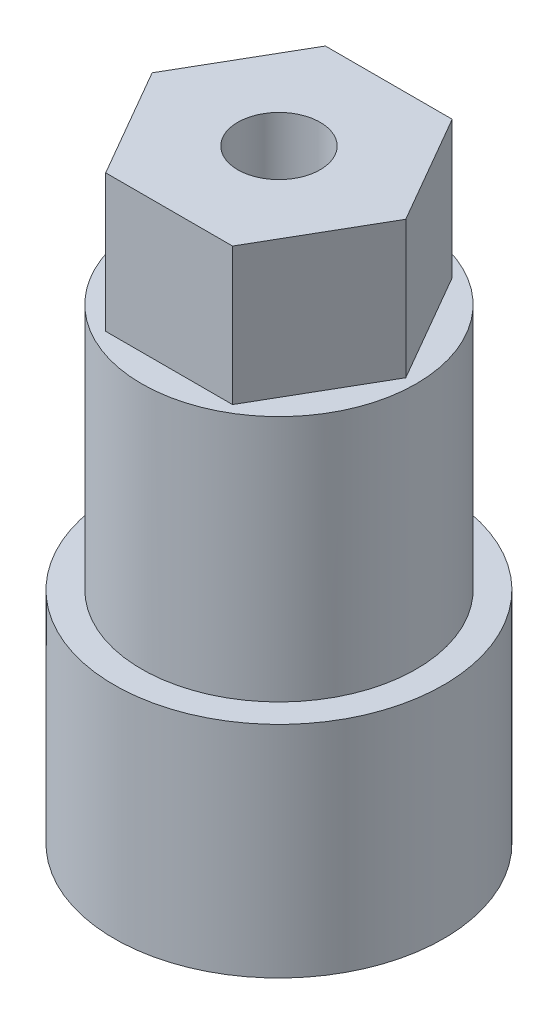
SolidWorks part; units mm, degrees
material "Nylon 101"
ref_plane "Front Plane" through (0, 0, 0) normal (0, 0, 1) x (1, 0, 0)
ref_plane "Top Plane" through (0, 0, 0) normal (0, 1, 0) x (1, 0, 0)
ref_plane "Right Plane" through (0, 0, 0) normal (1, 0, 0) x (0, 0, -1)
sketch "Sketch1" plane through (0, 0, 0) normal (0, 1, 0) x (1, 0, 0)
  circle A0 centre (0, 0) radius 5
  dimension "D1" = 10
extrude "Boss-Extrude1" add sketch "Sketch1" along normal blind 9
sketch "Sketch2" plane through (0, 0, 0) normal (0, -1, 0) x (1, 0, 0)
  circle A0 centre (0, 0) radius 6
  dimension "D1" = 12
extrude "Boss-Extrude2" add sketch "Sketch2" along normal blind 8
sketch "Sketch3" plane through (0, 9, 0) normal (0, 1, 0) x (1, 0, 0)
  line L1 (4.6188, 0) -> (2.3094, 4)
  line L2 (2.3094, 4) -> (-2.3094, 4)
  line L3 (-2.3094, 4) -> (-4.6188, 0)
  line L4 (-4.6188, 0) -> (-2.3094, -4)
  line L5 (-2.3094, -4) -> (2.3094, -4)
  line L6 (2.3094, -4) -> (4.6188, 0)
  circle A0 centre (0, 0) radius 4 construction
  dimension "D1" = 8
extrude "Boss-Extrude3" add sketch "Sketch3" along normal blind 5
sketch "Sketch4" plane through (0, 14, 0) normal (0, 1, 0) x (1, 0, 0)
  circle A0 centre (0, 0) radius 1.5
  dimension "D1" = 3
extrude "Cut-Extrude1" cut sketch "Sketch4" against normal blind 12
